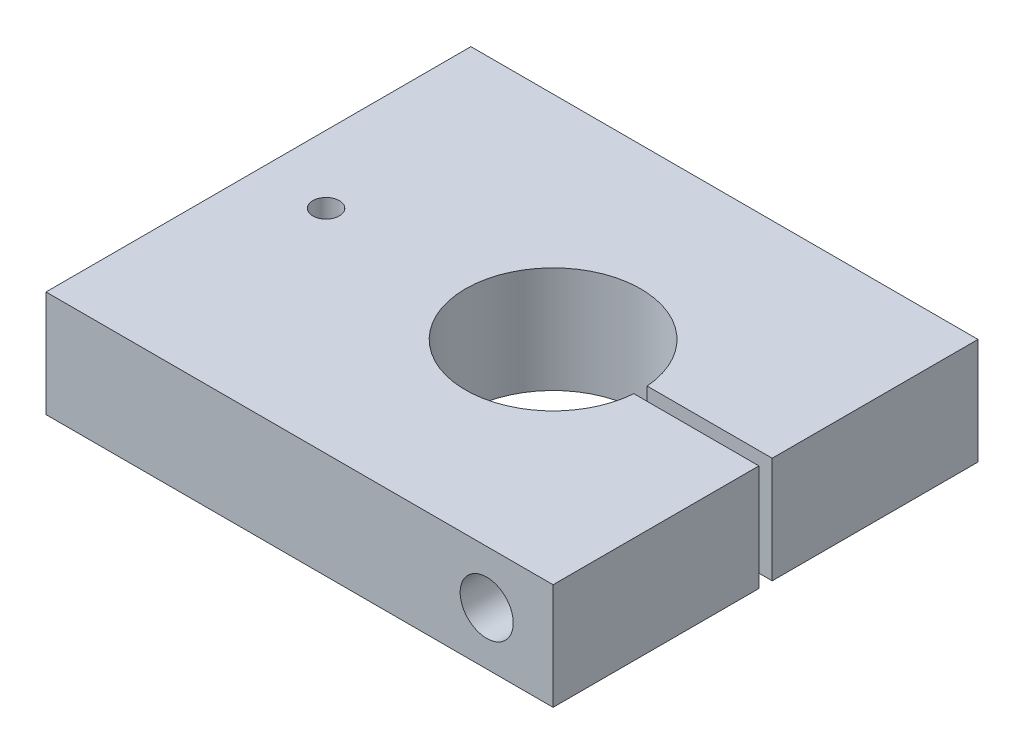
SolidWorks part; units mm, degrees
ref_plane "Front Plane" through (0, 0, 0) normal (0, 0, 1) x (1, 0, 0)
ref_plane "Top Plane" through (0, 0, 0) normal (0, 1, 0) x (1, 0, 0)
ref_plane "Right Plane" through (0, 0, 0) normal (1, 0, 0) x (0, 0, -1)
sketch "Sketch1" plane through (0, 0, 0) normal (0, 1, 0) x (1, 0, 0)
  line L0 (131.445, 50.8) -> (131.445, 0) construction
  line L1 (81.951, 0) -> (203.2, 0)
  line L3 (81.951, 101.6) -> (203.2, 101.6)
  line L4 (203.2, 0) -> (203.2, 101.6)
  line L5 (81.951, 101.6) -> (81.951, 0)
  circle A0 centre (152.4, 50.8) radius 20.955
  circle A2 centre (98.1075, 50.8) radius 3.175
  dimension "D3" = 50.8
  dimension "D4" = 50.8
  dimension "D6" = 41.91
  dimension "D1" = 101.6
  dimension "D2" = 50.8
extrude "Boss-Extrude1" add sketch "Sketch1" along normal blind 25.4
sketch "Sketch2" plane through (0, 0, 0) normal (0, 0, 1) x (1, 0, 0)
  line L0 (81.951, 25.4) -> (203.2, 25.4) construction
  line L1 (203.2, 25.4) -> (203.2, 0) construction
  circle A0 centre (187.325, 12.7) radius 6.35
  dimension "D1" = 12.7
  dimension "D2" = 15.875
extrude "Cut-Extrude1" cut sketch "Sketch2" against normal through all
sketch "Sketch3" plane through (0, 25.4, 0) normal (0, 1, 0) x (1, 0, 0)
  line L0 (203.2, 0) -> (203.2, 101.6) construction
  line L1 (203.2, 52.3875) -> (171.6456, 52.3875)
  line L2 (203.2, 52.3875) -> (203.2, 49.2125)
  line L3 (203.2, 49.2125) -> (171.6456, 49.2125)
  line L4 (171.6456, 52.3875) -> (171.6456, 49.2125)
  line L5 (81.951, 0) -> (203.2, 0) construction
  dimension "D1" = 3.175
  dimension "D2" = 49.2125
extrude "Cut-Extrude2" cut sketch "Sketch3" against normal through all
